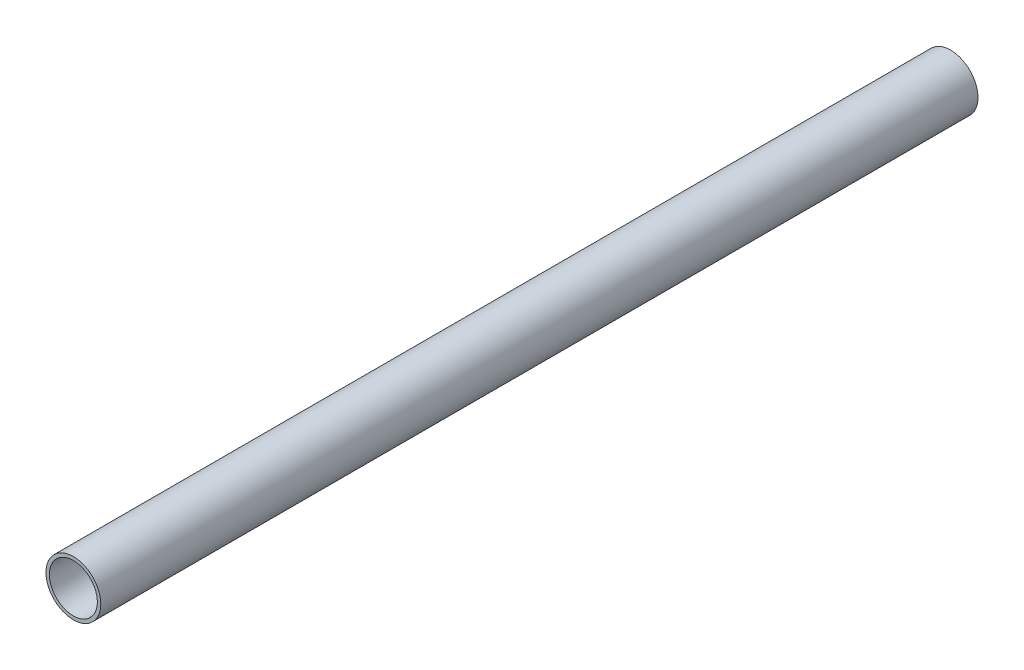
SolidWorks part; units mm, degrees
material "PVC Rigid"
ref_plane "Front Plane" through (0, 0, 0) normal (0, 0, 1) x (1, 0, 0)
ref_plane "Top Plane" through (0, 0, 0) normal (0, 1, 0) x (1, 0, 0)
ref_plane "Right Plane" through (0, 0, 0) normal (1, 0, 0) x (0, 0, -1)
sketch "Sketch1" plane through (0, 0, 0) normal (0, 0, 1) x (1, 0, 0)
  circle A0 centre (0, 0) radius 11.1125
  circle A1 centre (0, 0) radius 12.7
  dimension "D1" = 25.4
  dimension "D2" = 22.225
extrude "Boss-Extrude1" add sketch "Sketch1" along normal blind 406.4
